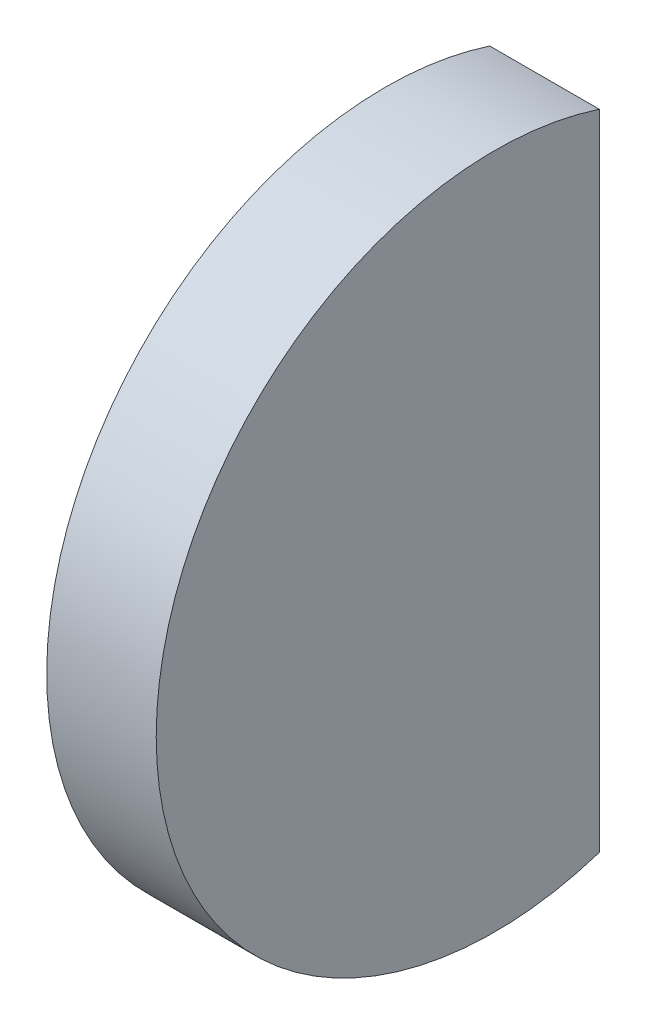
SolidWorks part; units mm, degrees
material "Стекло"
ref_plane "Front" through (0, 0, 0) normal (0, 0, 1) x (1, 0, 0)
ref_plane "Top" through (0, 0, 0) normal (0, 1, 0) x (1, 0, 0)
ref_plane "Right" through (0, 0, 0) normal (1, 0, 0) x (0, 0, -1)
sketch "Эскиз1" plane through (0, 0, 0) normal (0, 0, 1) x (1, 0, 0)
  line L0 (0, 0) -> (0, 16.6394) construction
  line L1 (1.941, 11) -> (5.5, 11)
  line L2 (5.5, 11) -> (5.5, 0)
  line L3 (5.5, 0) -> (0, 0)
  line L4 (0, 0) -> (12.8532, 0) construction
  arc A0 (0, 0) -> (1.941, 11) centre (32.14, 0) cw
  dimension "D1" = 32.14
  dimension "D2" = 22
  dimension "D3" = 5.5
revolve "Повернуть1" add sketch "Эскиз1" angle 360 about L4
sketch "Эскиз2" plane through (5.5, 0, 0) normal (1, 0, 0) x (0, 0, -1)
  line L0 (3.4, 10.4614) -> (3.4, -10.4614)
  line L1 (-11, 0) -> (-11, 10.4831) construction
  circle A0 centre (0, 0) radius 11 construction
  circle M1 centre (0, 0) radius 11
  dimension "D1" = 14.4
extrude "Вырез-Вытянуть1" cut sketch "Эскиз2" against normal through all contours L0 M1
